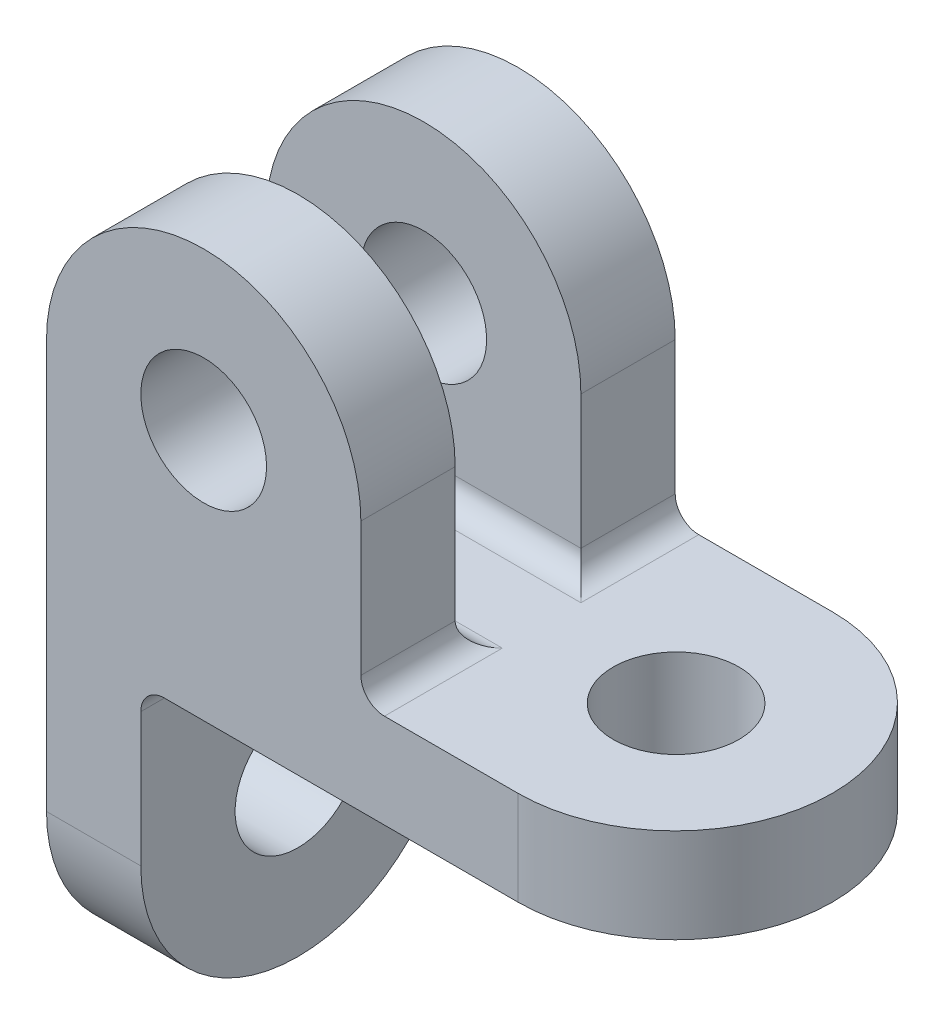
SolidWorks part; units mm, degrees
ref_plane "Front Plane" through (0, 0, 0) normal (0, 0, 1) x (1, 0, 0)
ref_plane "Top Plane" through (0, 0, 0) normal (0, 1, 0) x (1, 0, 0)
ref_plane "Right Plane" through (0, 0, 0) normal (1, 0, 0) x (0, 0, -1)
sketch "Sketch2" plane through (0, 0, 0) normal (0, 1, 0) x (1, 0, 0)
  line L1 (-30, 20) -> (30, 20)
  line L2 (-30, 20) -> (-30, -20)
  line L3 (-30, -20) -> (30, -20)
  line L5 (-30, 20) -> (30, -20) construction
  line L6 (-30, -20) -> (30, 20) construction
  arc A0 (30, -20) -> (30, 20) centre (30, 0) ccw
  point P0 (0, 0)
  dimension "D3" = 20
  dimension "D1" = 60
  dimension "D2" = 40
extrude "Boss-Extrude1" add sketch "Sketch2" along normal blind 12 contours L3 A0 L1 L2
sketch "Sketch3" plane through (0, 0, 20) normal (0, 0, 1) x (1, 0, 0)
  line L1 (-30, 12) -> (10, 12)
  line L2 (-30, 12) -> (-30, 32)
  line L3 (-30, 32) -> (10, 32)
  line L4 (10, 12) -> (10, 32)
  circle A1 centre (-10, 32) radius 20
  dimension "D1" = 20
extrude "Boss-Extrude11" add sketch "Sketch3" against normal blind 12
sketch "Sketch5" plane through (0, 0, -20) normal (0, 0, -1) x (-1, 0, 0)
  line L1 (30, 12) -> (-10, 12)
  line L2 (30, 12) -> (30, 32)
  line L3 (30, 32) -> (-10, 32)
  line L4 (-10, 12) -> (-10, 32)
  circle A0 centre (10, 32) radius 20
  line M3 (30, 12) -> (-30, 12)
extrude "Boss-Extrude12" add sketch "Sketch5" against normal blind 12 contours A0 L2 M3 | A0 L4 L1 | L3 A0 | L3 A0
sketch "Sketch6" plane through (-30, 0, 0) normal (-1, 0, 0) x (0, 0, 1)
  line L1 (-20, 0) -> (20, 0)
  line L2 (-20, 0) -> (-20, -20)
  line L3 (-20, -20) -> (20, -20)
  line L4 (20, 0) -> (20, -20)
  circle A0 centre (0, -20) radius 20
  line M1 (-20, 0) -> (20, 0)
  dimension "D1" = 20
extrude "Boss-Extrude13" add sketch "Sketch6" against normal blind 12 contours A0 L4 L1 | A0 L2 M1 | L3 A0 | L3 A0
sketch "Sketch8" plane through (0, 0, 20) normal (0, 0, 1) x (1, 0, 0)
  circle A0 centre (-10, 32) radius 8
extrude "Cut-Extrude1" cut sketch "Sketch8" against normal blind 128
sketch "Sketch9" plane through (0, 12, 0) normal (0, 1, 0) x (1, 0, 0)
  circle A1 centre (30.1305, -0.0176) radius 8
extrude "Cut-Extrude2" cut sketch "Sketch9" against normal blind 128 contours A1
sketch "Sketch10" plane through (-18, 0, 0) normal (1, 0, 0) x (0, 0, -1)
  circle A0 centre (0, -20) radius 8
extrude "Cut-Extrude4" cut sketch "Sketch10" against normal blind 128
fillet "Fillet4" radius 3 5 edges at (-18, 0, 0) (-10, 12, 8) (-10, 12, -8) (10, 12, -14) (10, 12, 14)
